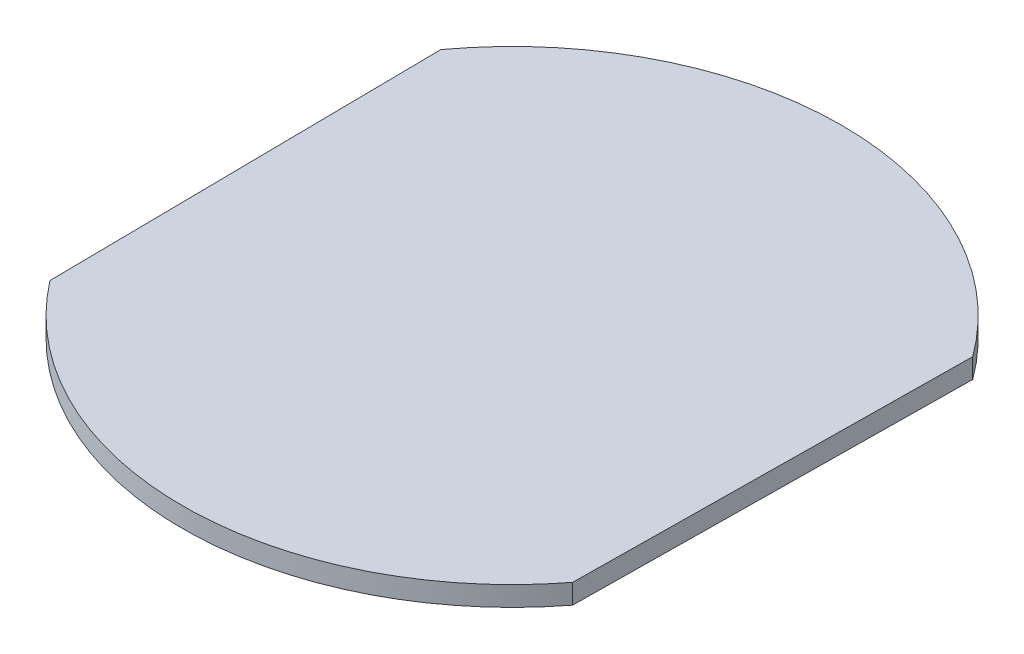
SolidWorks part; units mm, degrees
ref_plane "Front Plane" through (0, 0, 0) normal (0, 0, 1) x (1, 0, 0)
ref_plane "Top Plane" through (0, 0, 0) normal (0, 1, 0) x (1, 0, 0)
ref_plane "Right Plane" through (0, 0, 0) normal (1, 0, 0) x (0, 0, -1)
sketch "Sketch1" plane through (0, 0, 0) normal (0, 1, 0) x (1, 0, 0)
  line L0 (0, 0) -> (0, 24.3907) construction
  line L1 (39.6485, -30.463) -> (40.3461, 29.5329)
  line L2 (-39.6485, -30.463) -> (-40.3461, 29.5329)
  arc A0 (-39.6485, -30.463) -> (39.6485, -30.463) centre (0, 0) ccw
  arc A1 (40.3461, 29.5329) -> (-40.3461, 29.5329) centre (0, 0) ccw
extrude "Boss-Extrude1" add sketch "Sketch1" along normal mid plane 3
